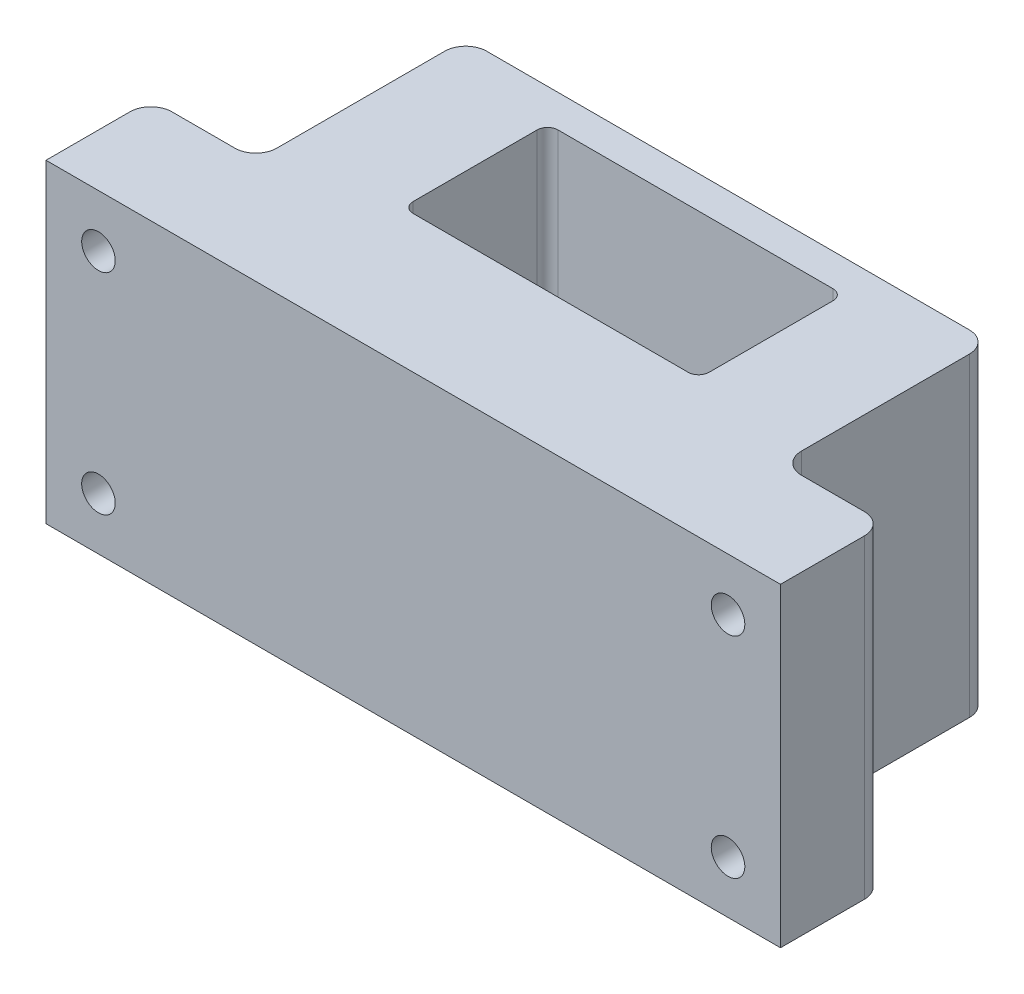
SolidWorks part; units mm, degrees
material "ABS"
ref_plane "前视基准面" through (0, 0, 0) normal (0, 0, 1) x (1, 0, 0)
ref_plane "上视基准面" through (0, 0, 0) normal (0, 1, 0) x (1, 0, 0)
ref_plane "右视基准面" through (0, 0, 0) normal (1, 0, 0) x (0, 0, -1)
sketch "草图1" plane through (0, 0, 0) normal (0, 0, 1) x (1, 0, 0)
  line L1 (0, 0) -> (70, 0)
  line L2 (0, 0) -> (0, 30)
  line L3 (0, 30) -> (70, 30)
  line L4 (70, 0) -> (70, 30)
  dimension "D1" = 30
  dimension "D2" = 70
extrude "凸台-拉伸1" add sketch "草图1" along normal blind 30
sketch "草图2" plane through (0, 0, 30) normal (0, 0, 1) x (1, 0, 0)
  line L0 (0, 15) -> (90.0237, 15) construction
  line L1 (0, 30) -> (0, 0) construction
  line L2 (35, 30) -> (35, -11.684) construction
  line L3 (70, 30) -> (0, 30) construction
  line L5 (5, 25) -> (65, 25) construction
  line L6 (5, 25) -> (5, 5) construction
  line L7 (5, 5) -> (65, 5) construction
  line L8 (65, 25) -> (65, 5) construction
  circle A0 centre (5, 5) radius 1.6
  circle A1 centre (65, 5) radius 1.6
  circle A2 centre (65, 25) radius 1.6
  circle A3 centre (5, 25) radius 1.6
  dimension "D3" = 3.2
  dimension "D1" = 20
  dimension "D2" = 60
extrude "切除-拉伸1" cut sketch "草图2" against normal through all
sketch "草图3" plane through (0, 0, 0) normal (0, -1, 0) x (1, 0, 0)
  line L0 (-18.345, 10) -> (106.0761, 10) construction
  line L2 (35, 30) -> (35, -9.9121) construction
  line L3 (0, 30) -> (70, 30) construction
  line L5 (20.9, 16.9) -> (49.1, 16.9)
  line L6 (20.9, 16.9) -> (20.9, 3.1)
  line L7 (20.9, 3.1) -> (49.1, 3.1)
  line L8 (49.1, 16.9) -> (49.1, 3.1)
  dimension "D1" = 13.8
  dimension "D2" = 28.2
  dimension "D3" = 20
extrude "切除-拉伸2" cut sketch "草图3" against normal through all
sketch "草图4" plane through (0, 0, 0) normal (0, -1, 0) x (1, 0, 0)
  line L2 (35, 16.9) -> (35, 3.1) construction
  line L3 (49.1, 16.9) -> (20.9, 16.9) construction
  line L4 (27.8, 10) -> (42.2, 10) construction
  line L5 (27.8, 16.9) -> (42.2, 16.9)
  line L6 (27.8, 3.1) -> (42.2, 3.1)
  line L7 (49.1, 3.1) -> (49.1, 16.9) construction
  line L8 (20.9, 3.1) -> (49.1, 3.1) construction
  line L9 (49.1, 3.1) -> (49.1, 16.9)
  line L10 (20.9, 3.1) -> (49.1, 3.1)
  line L11 (20.9, 16.9) -> (20.9, 3.1)
  line L12 (49.1, 16.9) -> (20.9, 16.9)
  arc A0 (27.8, 16.9) -> (27.8, 3.1) centre (27.8, 10) ccw
  arc A1 (42.2, 3.1) -> (42.2, 16.9) centre (42.2, 10) ccw
  point P10 (35, 10)
  line M7 (49.1, 3.1) -> (20.9, 3.1)
  line M8 (20.9, 3.1) -> (20.9, 16.9)
  line M9 (20.9, 16.9) -> (49.1, 16.9)
  line M10 (49.1, 16.9) -> (49.1, 3.1)
  dimension "D1" = 6.9
  dimension "D2" = 14.4
extrude "凸台-拉伸2" add sketch "草图4" against normal blind 1.2 contours A0 L11 M9 | A0 M8 M7 | A1 M10 M9 | A1 L9 M7
sketch "草图5" plane through (0, 0, 0) normal (0, 0, -1) x (-1, 0, 0)
  line L0 (0, 0) -> (-70, 0) construction
  line L1 (-35, 0) -> (-35, 46.268) construction
  circle A2 centre (-45.8, 11.1) radius 1.1
  circle A3 centre (-24.2, 11.1) radius 1.1
  dimension "D1" = 2.2
  dimension "D2" = 21.6
  dimension "D3" = 11.1
extrude "切除-拉伸3" cut sketch "草图5" against normal up to surface (3.1 mm away) up to face at (35, 8.1, 3.1)
sketch "草图6" plane through (0, 0, 0) normal (0, 0, -1) x (-1, 0, 0)
  line L0 (-60, 0) -> (-60, 30)
  line L1 (0, 0) -> (-70, 0) construction
  line L2 (-70, 30) -> (0, 30) construction
  line L3 (-35, 30) -> (-35, -7.3879) construction
  line L4 (-10, 0) -> (-10, 30)
  line L5 (-10, 0) -> (0, 0)
  line L6 (-60, 30) -> (-70, 30)
  line L9 (0, 0) -> (0, 30)
  line L10 (0, 30) -> (-70, 30)
  line L11 (-70, 30) -> (-70, 0)
  line L12 (-70, 0) -> (0, 0)
  line L13 (0, 0) -> (0, 30)
  line L14 (0, 30) -> (-10, 30)
  line L15 (-70, 30) -> (-70, 0)
  line L16 (-70, 0) -> (-60, 0)
  dimension "D2" = 10
  dimension "D1" = 0
extrude "切除-拉伸4" cut sketch "草图6" against normal blind 20
sketch "草图7" plane through (0, 0, 0) normal (0, -1, 0) x (1, 0, 0)
  line L0 (35, 30) -> (35, -12.9576) construction
  line L1 (0, 30) -> (70, 30) construction
  line L3 (42.2, 10) -> (27.8, 10) construction
  line L4 (60, 20) -> (60, 0) construction
  line L6 (54, 10) -> (54, 25) construction
  circle A0 centre (54, 10) radius 1.8
  circle A1 centre (16, 10) radius 1.8
  circle A2 centre (54, 25) radius 1.8
  circle A3 centre (16, 25) radius 1.8
  dimension "D1" = 3.6
  dimension "D2" = 6
  dimension "D3" = 2
  dimension "D4" = 15
extrude "切除-拉伸5" cut sketch "草图7" against normal blind 10.2
sketch "草图8" plane through (0, 0, 0) normal (0, -1, 0) x (1, 0, 0)
  line L0 (35, 30) -> (35, -5.5618) construction
  line L1 (0, 30) -> (70, 30) construction
  line L2 (54, 10) -> (54, 25) construction
  circle A0 centre (54, 10) radius 2.15
  circle A1 centre (16, 10) radius 2.15
  circle A2 centre (54, 25) radius 2.15
  circle A3 centre (16, 25) radius 2.15
  dimension "D1" = 4.3
  dimension "D3" = 15
  dimension "D2" = 2
extrude "切除-拉伸6" cut sketch "草图8" against normal blind 0.8
sketch "草图9" plane through (0, 0, 0) normal (0, 0, -1) x (-1, 0, 0)
  line L0 (-55.8, 10.2) -> (-52.2, 10.2) construction
  line L1 (-55.8, 10.2) -> (-52.2, 10.2) construction
  line L2 (-55.8, 10.2) -> (-52.2, 10.2) construction
  line L3 (-55.8, 10.2) -> (-52.2, 10.2) construction
  line L4 (-35, 30) -> (-35, -10.8846) construction
  line L5 (-60, 30) -> (-10, 30) construction
  line L6 (-54, 10.2) -> (-54, 48.5868) construction
  circle A0 centre (-54, 23) radius 1.8
  circle A1 centre (-16, 23) radius 1.8
  dimension "D1" = 3.6
  dimension "D2" = 7
extrude "切除-拉伸7" cut sketch "草图9" against normal blind 10.2
sketch "草图10" plane through (0, 0, 0) normal (0, 0, -1) x (-1, 0, 0)
  line L0 (-35, 30) -> (-35, -17.1834) construction
  line L1 (-60, 30) -> (-10, 30) construction
  circle A0 centre (-54, 23) radius 2.15
  circle A1 centre (-16, 23) radius 2.15
  dimension "D1" = 4.3
extrude "切除-拉伸8" cut sketch "草图10" against normal blind 0.8
fillet "圆角1" radius 2 6 edges at (60, 15, 0) (10, 15, 0) (70, 15, 20) (0, 15, 20) (10, 15, 20) (60, 15, 20)
fillet "圆角2" radius 1 4 edges at (20.9, 15.6, 16.9) (20.9, 15.6, 3.1) (49.1, 15.6, 3.1) (49.1, 15.6, 16.9)
